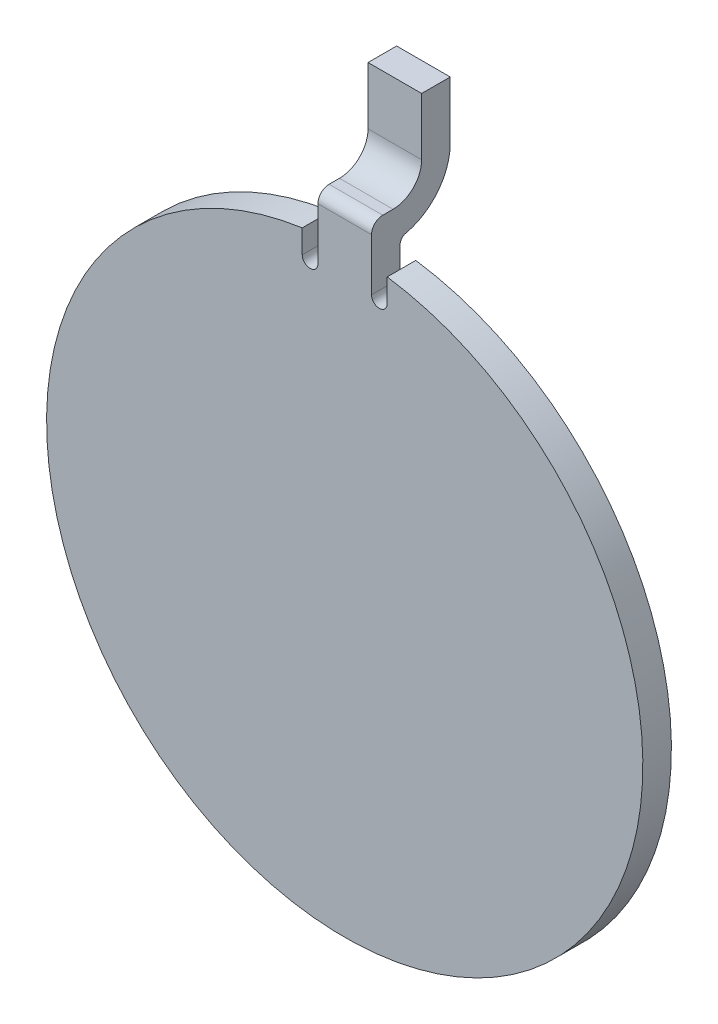
SolidWorks part; units mm, degrees
ref_plane "Front Plane" through (0, 0, 0) normal (0, 0, 1) x (1, 0, 0)
ref_plane "Top Plane" through (0, 0, 0) normal (0, 1, 0) x (1, 0, 0)
ref_plane "Right Plane" through (0, 0, 0) normal (1, 0, 0) x (0, 0, -1)
sketch "Sketch2" plane through (0, 0, 11.176) normal (0, 0, -1) x (-1, 0, 0)
  line L0 (0, 31.75) -> (0, 36.3927) construction
  line L1 (0, 37.0491) -> (0, 40.5675) construction
  line L3 (0.4765, 37.0276) -> (0.4765, 37.7055)
  line L4 (0.4765, 37.7055) -> (-0.4765, 37.7055)
  line L5 (-0.4765, 37.0276) -> (-0.4765, 37.7055)
  line L6 (0, 37.0491) -> (-0.4765, 37.7055) construction
  line L7 (0.4765, 37.7055) -> (0, 37.0491) construction
  arc A0 (-0.4765, 37.0276) -> (0.4765, 37.0276) centre (0, 31.75) ccw
  point P3 (0, 37.0491)
  dimension "D2" = 5.2991
  dimension "D1" = 0.953
  dimension "D3" = 5.9555
  dimension "D4" = 0.4765
extrude "Boss-Extrude1" add sketch "Sketch2" along normal blind 0.508
sketch "Sketch3" plane through (-0.4765, 0, 0) normal (-1, 0, 0) x (0, 0, 1)
  line L0 (11.176, 37.7055) -> (10.7929, 37.7055)
  line L1 (10.2849, 38.2135) -> (10.2849, 39.2339)
  arc A0 (10.7929, 37.7055) -> (10.2849, 38.2135) centre (10.7929, 38.2135) cw
  dimension "D1" = 0.508
extrude "Extrude-Thin1" add sketch "Sketch3" against normal up to vertex (0.953 mm away) thin thin type one direction reverse wall 0.508
fillet "Fillet1" radius 0.127 1 edges at (0, 37.2052, 10.668)
fillet "Fillet3" radius 0.2 1 edges at (0, 37.7055, 11.176)
sketch "Sketch4" plane through (0, 0, 10.668) normal (0, 0, -1) x (-1, 0, 0)
  line L0 (0.6158, 37.0839) -> (0.6158, 36.5802) construction
  line L1 (0.7551, 37.0839) -> (0.7551, 36.5802)
  line L2 (0.4765, 37.0839) -> (0.4765, 36.5802)
  line L3 (0, 31.75) -> (0, 35.3075) construction
  line L4 (0.4765, 37.0276) -> (0.4765, 37.0986) construction
  line L5 (-0.6158, 37.0839) -> (-0.6158, 36.5802) construction
  line L6 (-0.7551, 37.0839) -> (-0.7551, 36.5802)
  line L7 (-0.4765, 37.0839) -> (-0.4765, 36.5802)
  arc A1 (0.7551, 37.0839) -> (0.4765, 37.0839) centre (0.6158, 37.0839) ccw
  arc A2 (0.4765, 36.5802) -> (0.7551, 36.5802) centre (0.6158, 36.5802) ccw
  arc A3 (-0.7551, 37.0839) -> (-0.4765, 37.0839) centre (-0.6158, 37.0839) cw
  arc A4 (-0.4765, 36.5802) -> (-0.7551, 36.5802) centre (-0.6158, 36.5802) cw
  point P5 (0.6158, 36.832)
  point P18 (-0.6158, 36.832)
extrude "Cut-Extrude1" cut sketch "Sketch4" against normal through all
